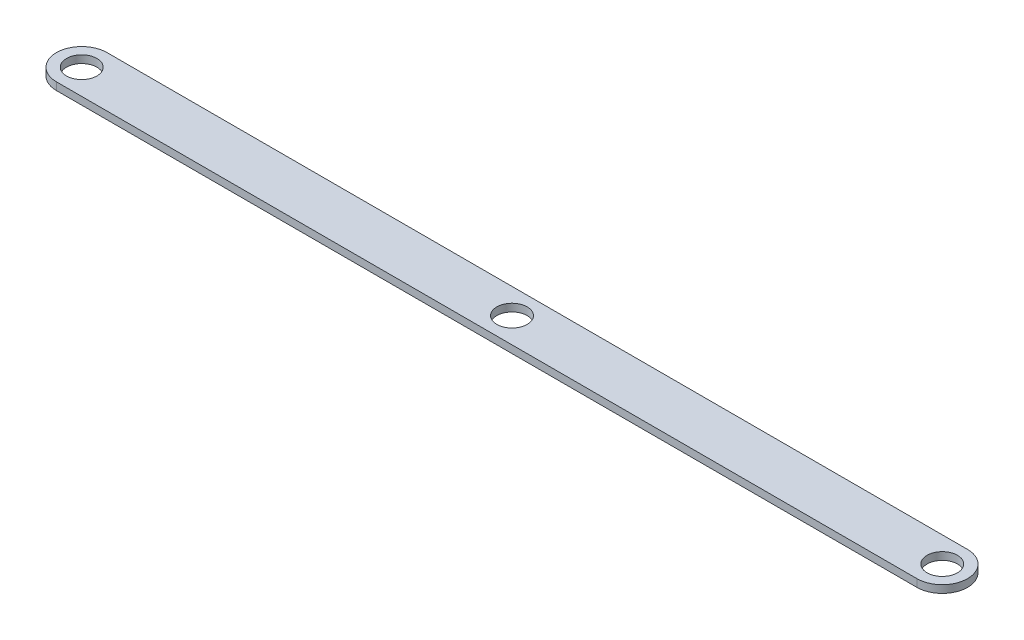
SolidWorks part; units mm, degrees
ref_plane "Front" through (0, 0, 0) normal (0, 0, 1) x (1, 0, 0)
ref_plane "Top" through (0, 0, 0) normal (0, 1, 0) x (1, 0, 0)
ref_plane "Right" through (0, 0, 0) normal (1, 0, 0) x (0, 0, -1)
sketch "Sketch1" plane through (0, 0, 0) normal (0, 1, 0) x (1, 0, 0)
  line L0 (-62.6876, 5.8571) -> (277.3124, 5.8571) construction
  line L1 (-62.6876, 15.8571) -> (277.3124, 15.8571)
  line L2 (-62.6876, -4.1429) -> (277.3124, -4.1429)
  arc A0 (-62.6876, 15.8571) -> (-62.6876, -4.1429) centre (-62.6876, 5.8571) ccw
  arc A1 (277.3124, -4.1429) -> (277.3124, 15.8571) centre (277.3124, 5.8571) ccw
  circle A2 centre (-62.6876, 5.8571) radius 6
  circle A3 centre (277.3124, 5.8571) radius 6
  circle A4 centre (107.3124, 5.8571) radius 6
  point P2 (107.3124, 5.8571)
  dimension "D1" = 20
  dimension "D2" = 340
extrude "Boss-Extrude1" add sketch "Sketch1" along normal blind 3
